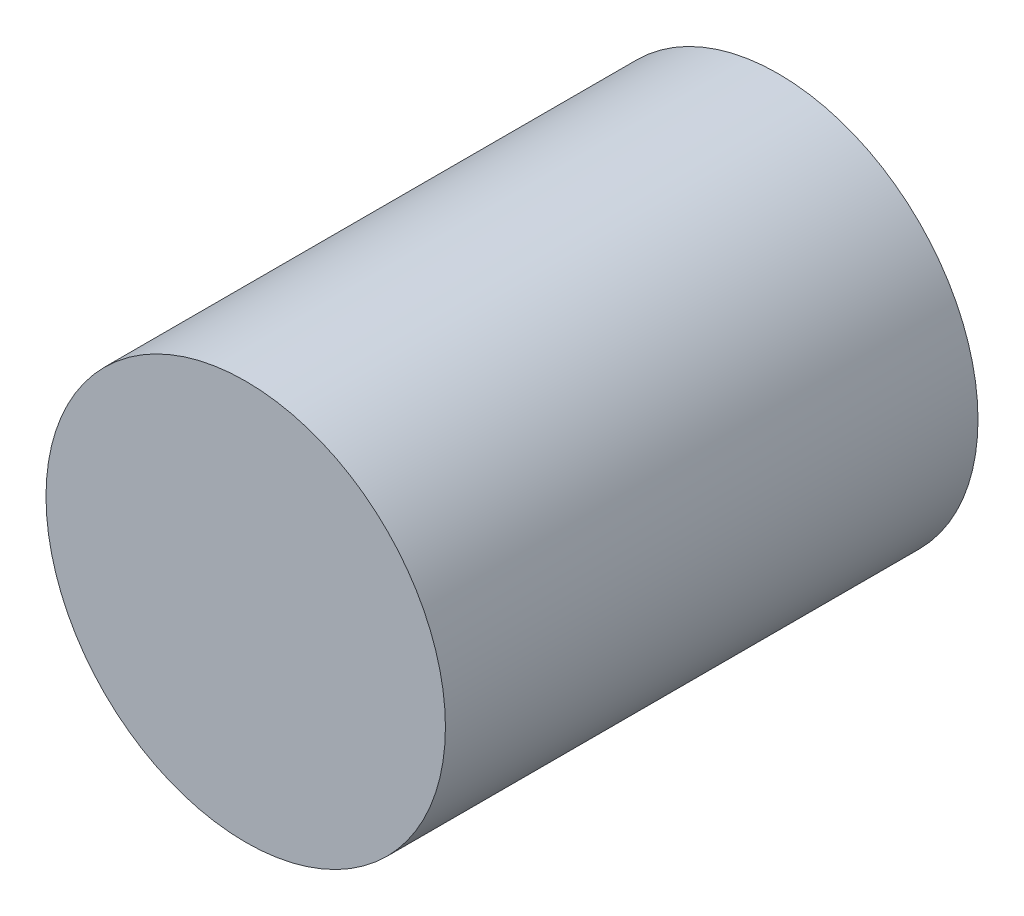
SolidWorks part; units mm, degrees
ref_plane "Front" through (0, 0, 0) normal (0, 0, 1) x (1, 0, 0)
ref_plane "Top" through (0, 0, 0) normal (0, 1, 0) x (-1, 0, 0)
ref_plane "Right" through (0, 0, 0) normal (1, 0, 0) x (0, 0, -1)
sketch "Sketch1" plane through (0, 0, 0) normal (0, 0, 1) x (1, 0, 0)
  circle A0 centre (0, 0) radius 4.7625
  dimension "D1" = 9.525
extrude "Base-Extrude" add sketch "Sketch1" along normal blind 12.7
